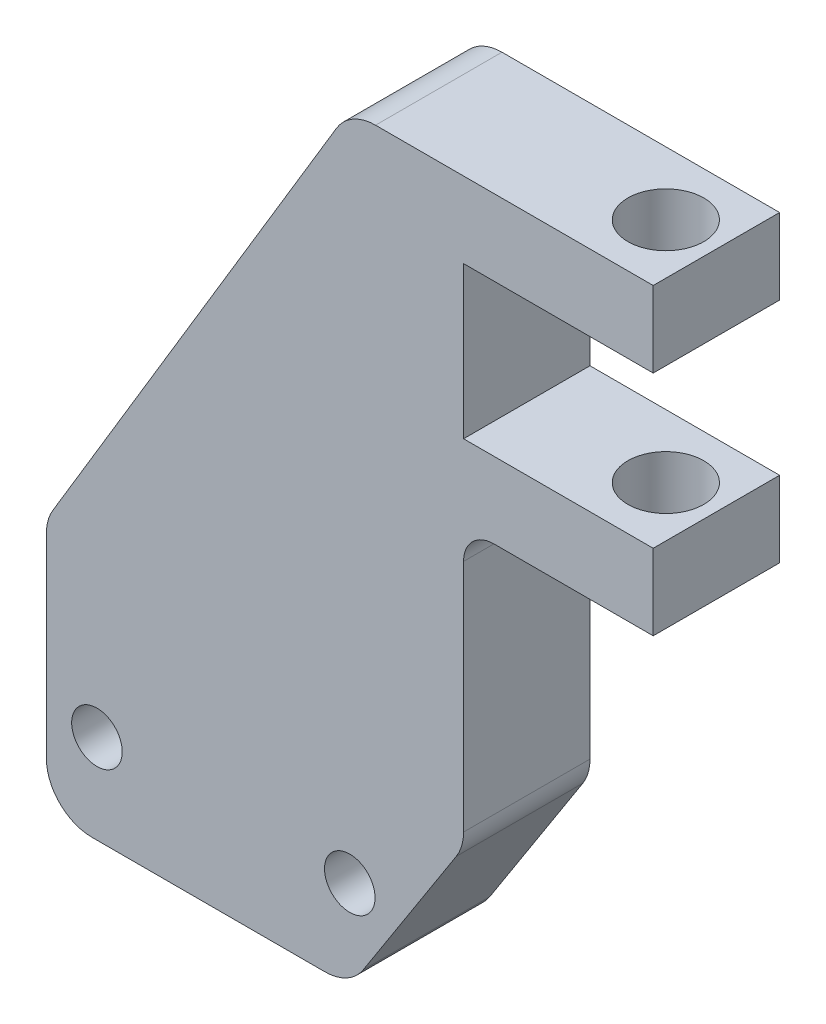
SolidWorks part; units mm, degrees
ref_plane "Front Plane" through (0, 0, 0) normal (0, 0, 1) x (1, 0, 0)
ref_plane "Top Plane" through (0, 0, 0) normal (0, 1, 0) x (1, 0, 0)
ref_plane "Right Plane" through (0, 0, 0) normal (1, 0, 0) x (0, 0, -1)
sketch "Sketch1" plane through (0, 0, 0) normal (0, 0, 1) x (1, 0, 0)
  line L0 (7.0386, 6.2133) -> (7.0386, 16.2133)
  line L1 (7.0386, 16.2133) -> (19.0386, 36.2133)
  line L2 (19.0386, 36.2133) -> (31.0386, 36.2133)
  line L3 (31.0386, 36.2133) -> (31.0386, 33.2133)
  line L4 (31.0386, 33.2133) -> (23.5386, 33.2133)
  line L5 (23.5386, 33.2133) -> (23.5386, 27.2133)
  line L6 (23.5386, 27.2133) -> (31.0386, 27.2133)
  line L7 (31.0386, 27.2133) -> (31.0386, 24.2133)
  line L8 (31.0386, 24.2133) -> (23.5386, 24.2133)
  line L9 (23.5386, 24.2133) -> (23.5386, 13.2133)
  line L10 (23.5386, 13.2133) -> (19.0386, 6.2133)
  line L11 (19.0386, 6.2133) -> (7.0386, 6.2133)
  circle A0 centre (9.0386, 9.7382) radius 1
  circle A1 centre (19.0386, 9.7382) radius 1
  dimension "D10" = 2
  dimension "D1" = 3
  dimension "D2" = 3
  dimension "D3" = 6
  dimension "D4" = 30
  dimension "D5" = 12
  dimension "D6" = 7.5
  dimension "D7" = 11
  dimension "D8" = 24
  dimension "D9" = 12
  dimension "D11" = 10
  dimension "D12" = 2
extrude "Extrude1" add sketch "Sketch1" along normal blind 5
fillet "Fillet2" radius 1.8 5 edges at (19.0386, 36.2133, 2.5) (7.0386, 16.2133, 2.5) (23.5386, 13.2133, 2.5) (19.0386, 6.2133, 2.5) (7.0386, 6.2133, 2.5)
fillet "Fillet3" radius 1.2 1 edges at (23.5386, 24.2133, 2.5)
sketch "Sketch3" plane through (0, 36.2133, 0) normal (0, 1, 0) x (1, 0, 0)
  line L0 (31.0386, -5) -> (31.0386, 0) construction
  circle A0 centre (29.0386, -2.5) radius 1.5
  dimension "D1" = 3
  dimension "D2" = 2
extrude "Extrude2" cut sketch "Sketch3" against normal blind 17
